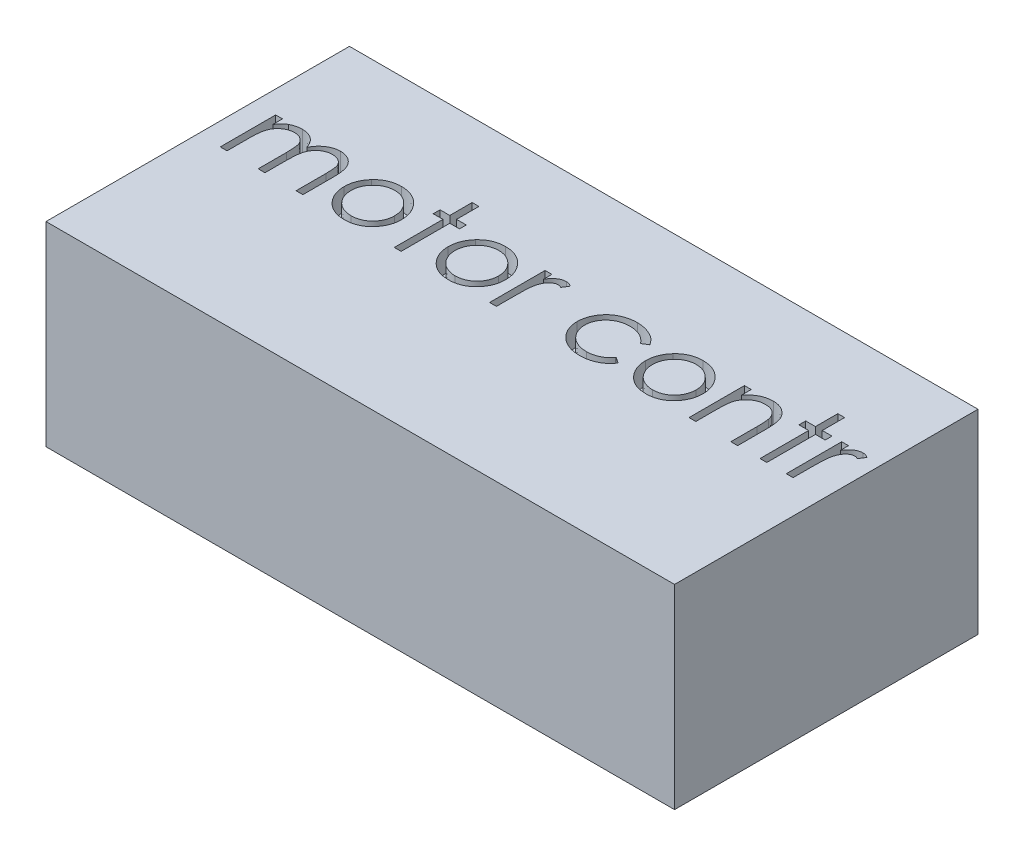
SolidWorks part; units mm, degrees
ref_plane "Front Plane" through (0, 0, 0) normal (0, 0, 1) x (1, 0, 0)
ref_plane "Top Plane" through (0, 0, 0) normal (0, 1, 0) x (1, 0, 0)
ref_plane "Right Plane" through (0, 0, 0) normal (1, 0, 0) x (0, 0, -1)
sketch "Sketch1" plane through (0, 0, 0) normal (0, 1, 0) x (1, 0, 0)
  line L1 (-14.5, -7) -> (14.5, -7)
  line L2 (-14.5, -7) -> (-14.5, 7)
  line L3 (-14.5, 7) -> (14.5, 7)
  line L4 (14.5, -7) -> (14.5, 7)
  line L5 (-14.5, -7) -> (14.5, 7) construction
  line L6 (-14.5, 7) -> (14.5, -7) construction
  point P0 (0, 0)
  dimension "D1" = 29
  dimension "D2" = 14
extrude "Boss-Extrude1" add sketch "Sketch1" along normal blind 9
sketch "Sketch2" plane through (0, 9, 0) normal (0, 1, 0) x (1, 0, 0)
  line L0 (-14.5, 0) -> (14.5, 0) construction
  line L1 (14.5, -7) -> (14.5, 7) construction
  text T0 "motor contr"
  point P6 (0, 0)
extrude "Cut-Extrude1" cut sketch "Sketch2" against normal blind 1
